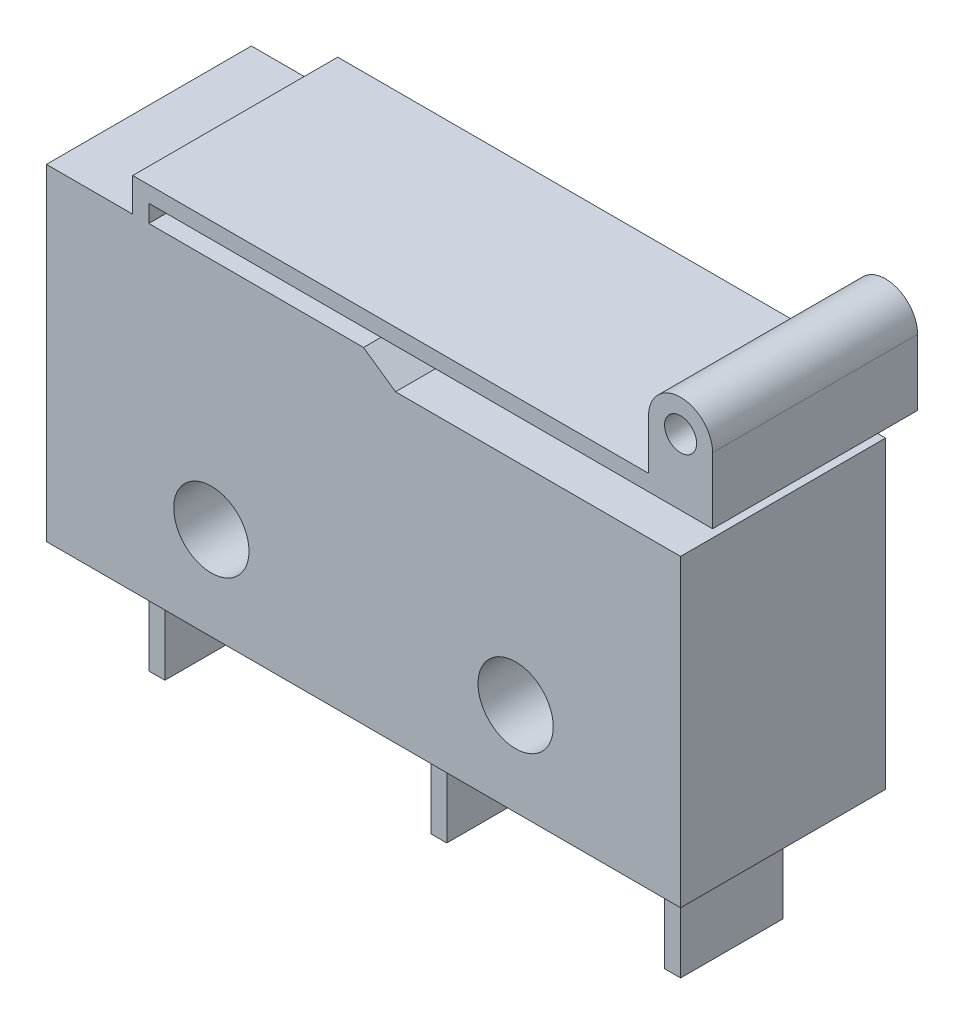
SolidWorks part; units mm, degrees
ref_plane "Front Plane" through (0, 0, 0) normal (0, 0, 1) x (1, 0, 0)
ref_plane "Top Plane" through (0, 0, 0) normal (0, 1, 0) x (1, 0, 0)
ref_plane "Right Plane" through (0, 0, 0) normal (1, 0, 0) x (0, 0, -1)
sketch "Sketch1" plane through (0, 0, 0) normal (0, 0, 1) x (1, 0, 0)
  line L0 (2.1, 0) -> (10.4, 0)
  line L1 (0, 0) -> (1.6, 0)
  line L2 (0, 0) -> (0, 10.2)
  line L3 (0, 10.2) -> (2.6957, 10.2)
  line L4 (19.8, 0) -> (19.8, 10.2)
  line L6 (1.6, 0) -> (1.6, -3.5)
  line L7 (1.6, -3.5) -> (2.1, -3.5)
  line L8 (2.1, 0) -> (2.1, -3.5)
  line L10 (10.4, 0) -> (10.4, -3.5)
  line L11 (10.4, -3.5) -> (10.9, -3.5)
  line L12 (10.9, 0) -> (10.9, -3.5)
  line L14 (17.7, 0) -> (17.7, -3.5)
  line L15 (17.7, -3.5) -> (18.2, -3.5)
  line L16 (18.2, 0) -> (18.2, -3.5)
  line L17 (10.9, 0) -> (17.7, 0)
  line L18 (18.2, 0) -> (19.8, 0)
  line L19 (3.1957, 10.2) -> (3.1957, 10.7463)
  line L20 (3.1957, 10.7463) -> (20.8, 10.7463)
  line L21 (20.8, 12.8032) -> (20.8, 10.7463)
  line L22 (18.8, 12.8032) -> (18.8, 11.2463)
  line L23 (18.8, 11.2463) -> (2.6957, 11.2463)
  line L24 (2.6957, 11.2463) -> (2.6957, 10.2)
  line L25 (3.1957, 10.2) -> (19.8, 10.2)
  circle A0 centre (5.15, 2.9) radius 1.175
  circle A1 centre (14.65, 2.9) radius 1.175
  circle A2 centre (19.8, 12.8032) radius 0.5
  arc A3 (20.8, 12.8032) -> (18.8, 12.8032) centre (19.8, 12.8032) ccw
  point P21 (1.85, -3.5)
  point P22 (10.65, -3.5)
  point P23 (17.95, -3.5)
  dimension "D2" = 2.35
  dimension "D3" = 2.35
  dimension "D17" = 1
  dimension "D18" = 2
  dimension "D1" = 10.2
  dimension "D4" = 9.5
  dimension "D5" = 5.15
  dimension "D6" = 2.9
  dimension "D7" = 6.4
  dimension "D8" = 1.85
  dimension "D9" = 0.5
  dimension "D10" = 6.4
  dimension "D11" = 0.5
  dimension "D12" = 6.4
  dimension "D13" = 0.5
  dimension "D14" = 7.3
  dimension "D15" = 8.8
  dimension "D16" = 19.8
  dimension "D19" = 0.5
  dimension "D20" = 0.5
extrude "Boss-Extrude1" add sketch "Sketch1" along normal blind 6.4
sketch "Sketch2" plane through (0, 0, 0) normal (-1, 0, 0) x (0, 0, 1)
  line L0 (6.4, -3.5) -> (0, -3.5) construction
  line L1 (0, 0) -> (1.6, 0)
  line L2 (0, 0) -> (0, -3.5)
  line L3 (0, -3.5) -> (1.6, -3.5)
  line L4 (1.6, 0) -> (1.6, -3.5)
  line L6 (6.4, 0) -> (4.8, 0)
  line L7 (6.4, 0) -> (6.4, -3.5)
  line L8 (6.4, -3.5) -> (4.8, -3.5)
  line L9 (4.8, 0) -> (4.8, -3.5)
  point P12 (3.2, -3.5)
  dimension "D1" = 3.2
  dimension "D2" = 1.6
extrude "Cut-Extrude1" cut sketch "Sketch2" against normal through all
sketch "Sketch3" plane through (0, 0, 6.4) normal (0, 0, 1) x (1, 0, 0)
  line L0 (19.8, 9.5) -> (10.9, 9.5)
  line L1 (19.8, 0) -> (19.8, 10.2) construction
  line L2 (10.9, 9.5) -> (9.9, 10.2)
  line L4 (19.8, 10.2) -> (3.1957, 10.2) construction
  line L5 (9.9, 10.2) -> (19.8, 10.2)
  line L6 (19.8, 10.2) -> (19.8, 9.5)
  dimension "D1" = 9.5
  dimension "D2" = 1
extrude "Cut-Extrude2" cut sketch "Sketch3" against normal through all
